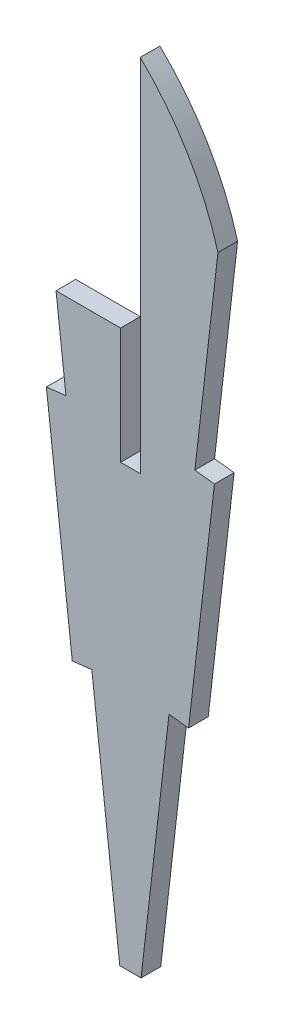
SolidWorks part; units mm, degrees
ref_plane "Front Plane" through (0, 0, 0) normal (0, 0, 1) x (1, 0, 0)
ref_plane "Top Plane" through (0, 0, 0) normal (0, 1, 0) x (1, 0, 0)
ref_plane "Right Plane" through (0, 0, 0) normal (1, 0, 0) x (0, 0, -1)
sketch "Sketch1" plane through (0, 0, 0) normal (0, 0, 1) x (1, 0, 0)
  line L0 (0, -185.0621) -> (-1.524, -185.0621)
  line L1 (5.7429, -182.883) -> (3.7396, -200.2526)
  line L2 (-1.524, -185.0621) -> (-1.524, -157.1523)
  line L3 (2.2257, -200.078) -> (3.7396, -200.2526)
  line L4 (-7.5376, -167.2346) -> (-5.7529, -182.7084)
  line L5 (-3.7497, -200.078) -> (-1.5851, -218.846)
  line L6 (-5.7529, -182.7084) -> (-7.2669, -182.883)
  line L7 (-3.7497, -200.078) -> (-5.2636, -200.2526)
  line L8 (-0.762, -185.0621) -> (-0.762, -247.1656) construction
  line L9 (-7.2669, -182.883) -> (-5.2636, -200.2526)
  line L10 (-1.5851, -218.846) -> (0.0611, -218.846)
  line L11 (4.2289, -182.7084) -> (5.7429, -182.883)
  line L12 (2.2257, -200.078) -> (0.0611, -218.846)
  line L13 (6.0136, -167.2346) -> (4.2289, -182.7084)
  line L14 (0, -185.0621) -> (0, -157.1523)
  arc A0 (-7.5376, -167.2346) -> (-1.524, -157.1523) centre (14.0358, -173.2675) cw
  arc A1 (6.0136, -167.2346) -> (0, -157.1523) centre (-15.5598, -173.2675) ccw
  point P21 (-0.762, -219.2285)
  point P26 (-0.762, -185.0621)
extrude "Boss-Extrude1" add sketch "Sketch1" along normal blind 1.524
sketch "Sketch2" plane through (0, 0, 1.524) normal (0, 0, 1) x (1, 0, 0)
  line L0 (-1.524, -185.0621) -> (-1.524, -157.1523) construction
  line L2 (-1.524, -176.0592) -> (-11.864, -176.0592)
  line L3 (-1.524, -176.0592) -> (-1.524, -155.0511)
  line L4 (-1.524, -155.0511) -> (-11.864, -155.0511)
  line L5 (-11.864, -176.0592) -> (-11.864, -155.0511)
extrude "Cut-Extrude1" cut sketch "Sketch2" against normal blind 1.524
